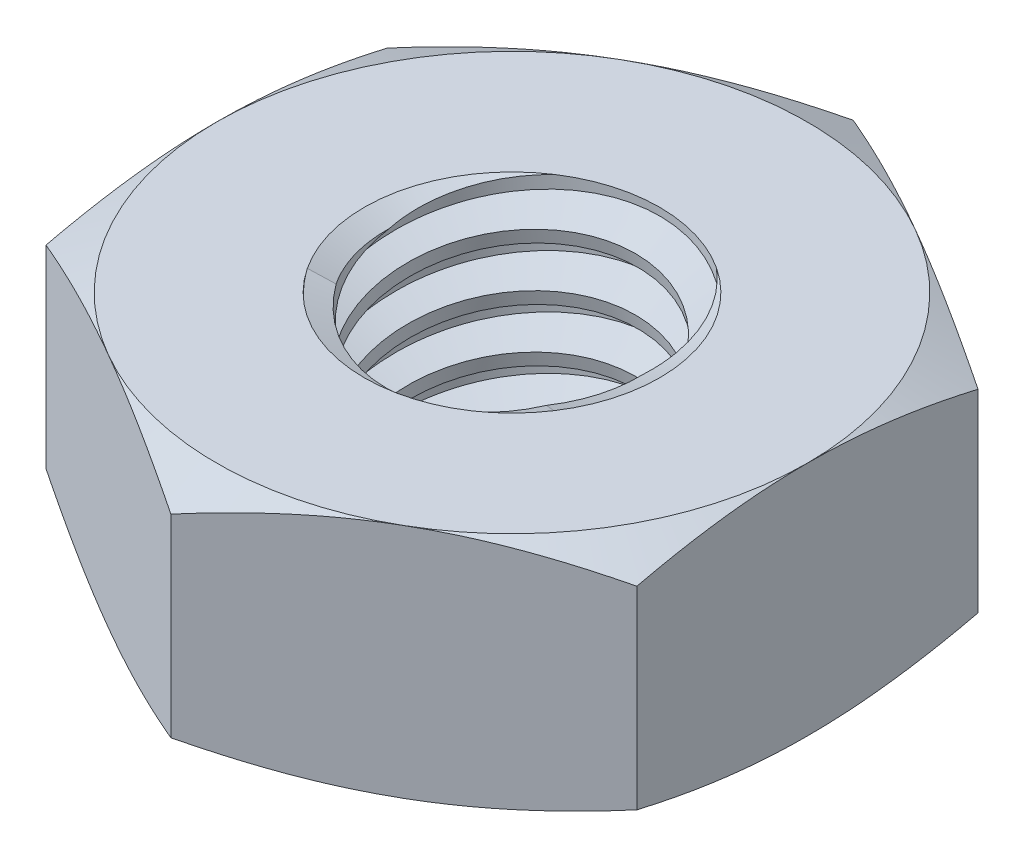
SolidWorks part; units mm, degrees
ref_plane "Front" through (0, 0, 0) normal (0, 0, 1) x (1, 0, 0)
ref_plane "Top" through (0, 0, 0) normal (0, 1, 0) x (1, 0, 0)
ref_plane "Right" through (0, 0, 0) normal (1, 0, 0) x (0, 0, -1)
sketch "Sketch1" plane through (0, 0, 0) normal (0, 1, 0) x (1, 0, 0)
  line L1 (0, 2.8868) -> (-2.5, 1.4434)
  line L2 (-2.5, 1.4434) -> (-2.5, -1.4434)
  line L3 (-2.5, -1.4434) -> (0, -2.8868)
  line L4 (0, -2.8868) -> (2.5, -1.4434)
  line L5 (2.5, -1.4434) -> (2.5, 1.4434)
  line L6 (2.5, 1.4434) -> (0, 2.8868)
  circle A0 centre (0, 0) radius 2.5 construction
  dimension "Hex Flats" = 5
extrude "Extrude1" add sketch "Sketch1" along normal mid plane 2
sketch "Sketch2" plane through (0, 0, 0) normal (1, 0, 0) x (0, 0, -1)
  line L0 (-1.25, -1) -> (-1.25, 1) construction
  line L1 (0, -1) -> (1.25, -1)
  line L2 (0, -1) -> (0, 1)
  line L3 (0, 1) -> (1.25, 1)
  line L4 (1.25, -1) -> (1.25, 1)
  line L5 (-1.4434, 1) -> (1.4434, 1) construction
  line L6 (-1.4434, -1) -> (1.4434, -1) construction
  line L7 (0, -2.25) -> (0, -1) construction
  dimension "Thread Dia" = 2.5
revolve "Revolve1" add sketch "Sketch2" angle 360 about L7
sketch "Sketch3" plane through (0, 0, 0) normal (1, 0, 0) x (0, 0, -1)
  line L0 (1.25, 1) -> (-1.25, 1) construction
  line L1 (-1.25, 1) -> (-1.25, 0.55) construction
  line L2 (-1.25, 0.55) -> (1.25, 1) construction
  line L3 (1.25, 1) -> (1.26, 0.9446) construction
  line L4 (1.26, 0.9446) -> (1.3297, 0.5571)
  line L5 (1.3297, 0.5571) -> (1.0651, 0.6524)
  line L6 (1.0651, 0.6524) -> (1.0452, 0.7631)
  line L7 (1.0452, 0.7631) -> (1.26, 0.9446)
  line L8 (1.0551, 0.7077) -> (1.2948, 0.7509) construction
  line L9 (1.25, 1) -> (1.25, 0.7428) construction
  line L10 (1.25, 0.7428) -> (-1.25, 0.2928) construction
  line L11 (-1.25, 0.2928) -> (-1.25, 0.55) construction
  line L12 (-0.0868, 1) -> (0.0868, 0.0356) construction
  line L13 (-1.25, -1) -> (-1.25, 1) construction
  line L14 (0, 1) -> (1.25, 1) construction
  line L15 (1.25, -1) -> (1.25, 1) construction
  line L16 (0, 0) -> (0, 1) construction
  line L17 (-1.26, 0.9446) -> (-1.3297, 0.5571) construction
  line L18 (-1.0452, 0.7631) -> (-1.26, 0.9446) construction
  line L19 (-1.0651, 0.6524) -> (-1.0452, 0.7631) construction
  line L20 (-1.3297, 0.5571) -> (-1.0651, 0.6524) construction
  line L21 (0.0868, 1) -> (-0.0868, 0.0356) construction
  point P13 (0, 0.5178)
  dimension "D1" = 0.0563
  dimension "D2" = 0.1125
  dimension "Thread Pitch" = 0.45
  dimension "D4" = 60
  dimension "D5" = 0.45
revolve "Cut-Revolve1" cut sketch "Sketch3" angle 360 about L12
pattern_linear "LPattern1" count 4 spacing 0.45 along (0, -1, 0) count 2 spacing 0.45 along (0, 1, 0) of "Cut-Revolve1"
sketch "Sketch4" plane through (0, 0, 0) normal (1, 0, 0) x (0, 0, -1)
  line L0 (0, 1) -> (1.25, 1)
  line L1 (1.25, 1) -> (1.0452, 0.9045)
  line L2 (1.0452, 0.9045) -> (1.0452, -0.9045)
  line L3 (1.0452, -0.9045) -> (1.25, -1)
  line L4 (1.25, -1) -> (0, -1)
  line L5 (0, -1) -> (0, 1)
  line L6 (1.25, -1) -> (1.25, 1) construction
  line L7 (0, 1) -> (1.25, 1) construction
  line L8 (0, -1) -> (1.25, -1) construction
  line L9 (0, -1) -> (0, 1) construction
  line L10 (0, 1) -> (0, 1.226) construction
  dimension "D1" = 25
revolve "Cut-Revolve2" cut sketch "Sketch4" angle 360 about L10
combine bodies "Combine1" operation type subtract main body 112 bodies to subtract 111
sketch "Sketch5" plane through (0, 0, 0) normal (1, 0, 0) x (0, 0, -1)
  line L0 (0, -1) -> (2.5, -1)
  line L1 (2.5, -1) -> (2.8868, -0.8197)
  line L2 (2.8868, -0.8197) -> (2.8868, 0.8197)
  line L3 (2.8868, 0.8197) -> (2.5, 1)
  line L4 (0, 1) -> (0, 2.27)
  line L5 (0, 2.27) -> (4.1568, 2.27)
  line L6 (4.1568, 2.27) -> (4.1568, -2.27)
  line L7 (4.1568, -2.27) -> (0, -2.27)
  line L8 (0, -2.27) -> (0, -1)
  line L9 (2.5, 1) -> (2.5, -1) construction
  line L11 (0, -1) -> (1.25, -1) construction
  line L12 (2.5, 1) -> (0, 1)
  line L13 (2.8868, 0) -> (4.1568, 0) construction
  line L14 (2.8868, 1) -> (2.8868, -1) construction
  line L15 (0, -1) -> (0, 1) construction
  line L17 (0, 0) -> (2.5, 0) construction
  line L22 (0, 1) -> (1.25, 1) construction
  dimension "D1" = 25
  dimension "D2" = 1.27
  dimension "D3" = 2
revolve "Cut-Revolve3" cut sketch "Sketch5" angle 360 about L15
equation "\"D1@Sketch3\"=\"Thread Pitch@Sketch3\"/8"
equation "\"D2@Sketch3\"=\"Thread Pitch@Sketch3\"/4"
equation "\"D5@Sketch3\"=\"Thread Pitch@Sketch3\""
equation "\"D4@LPattern1\"=\"Thread Pitch@Sketch3\""
equation "\"D3@LPattern1\"=\"Thread Pitch@Sketch3\""
equation "\"D1@LPattern1\"=\"Height@Extrude1\"/\"Thread Pitch@Sketch3\""
